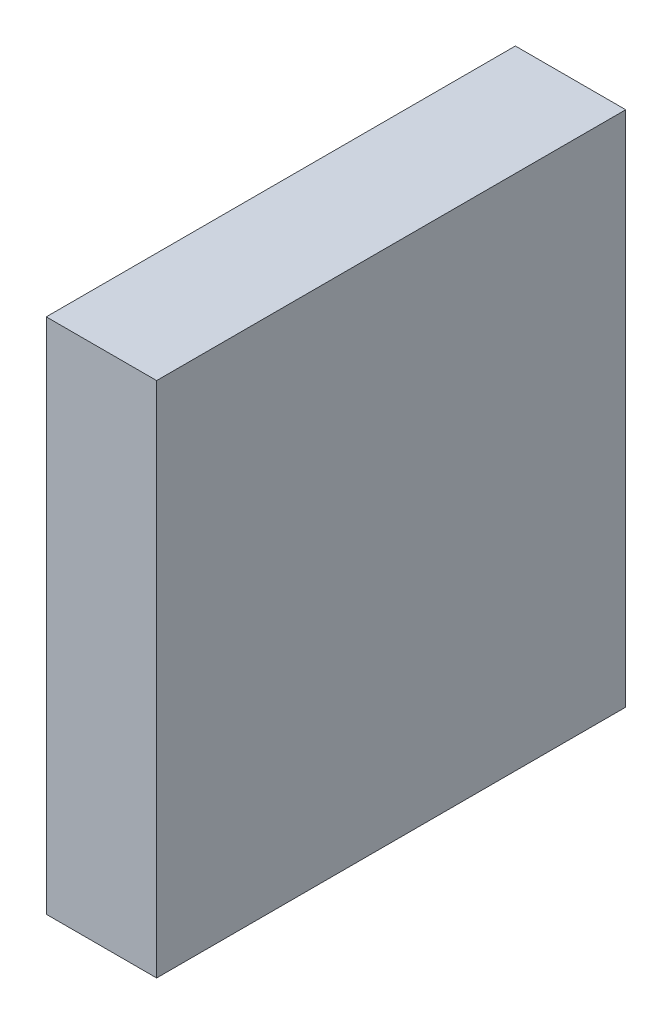
SolidWorks part; units mm, degrees
ref_plane "Alzado" through (0, 0, 0) normal (0, 0, 1) x (1, 0, 0)
ref_plane "Planta" through (0, 0, 0) normal (0, 1, 0) x (1, 0, 0)
ref_plane "Vista lateral" through (0, 0, 0) normal (1, 0, 0) x (0, 0, -1)
sketch "Croquis1" plane through (0, 0, 0) normal (0, 0, 1) x (1, 0, 0)
  line L1 (-8, 37.5) -> (8, 37.5)
  line L2 (-8, 37.5) -> (-8, -37.5)
  line L3 (-8, -37.5) -> (8, -37.5)
  line L4 (8, 37.5) -> (8, -37.5)
  line L5 (-8, 37.5) -> (8, -37.5) construction
  line L6 (-8, -37.5) -> (8, 37.5) construction
  point P0 (0, 0)
  dimension "D1" = 16
  dimension "D2" = 75
extrude "Saliente-Extruir1" add sketch "Croquis1" along normal blind 68
